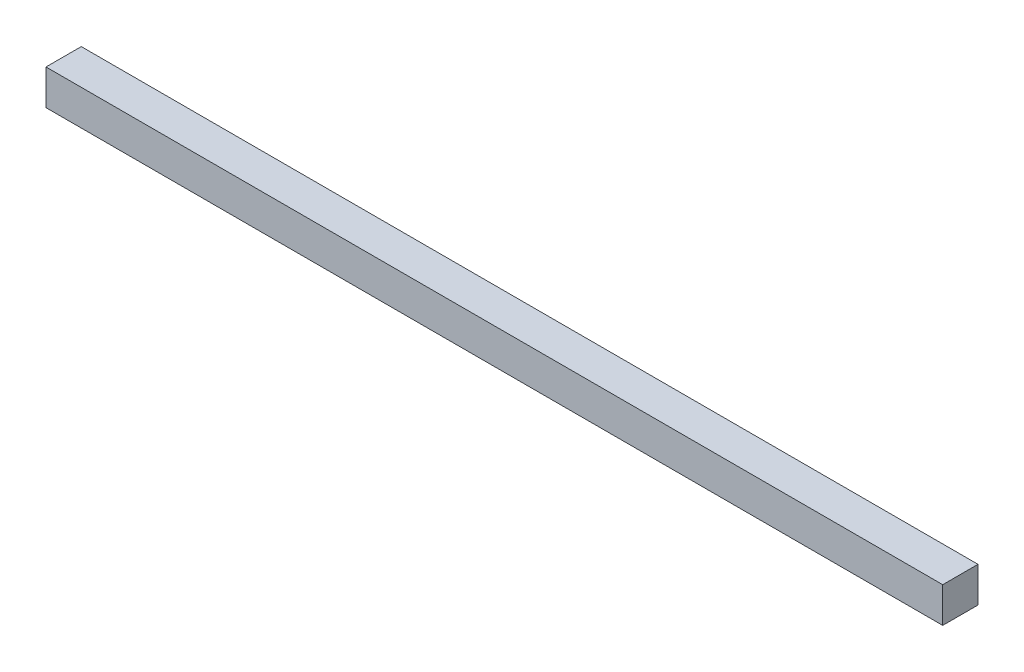
SolidWorks part; units mm, degrees
ref_plane "Front Plane" through (0, 0, 0) normal (0, 0, 1) x (1, 0, 0)
ref_plane "Top Plane" through (0, 0, 0) normal (0, 1, 0) x (1, 0, 0)
ref_plane "Right Plane" through (0, 0, 0) normal (1, 0, 0) x (0, 0, -1)
sketch "Sketch1" plane through (0, 0, 0) normal (0, 0, 1) x (1, 0, 0)
  line L1 (0, 0) -> (76.25, 0)
  line L2 (0, 0) -> (0, 3)
  line L3 (0, 3) -> (76.25, 3)
  line L4 (76.25, 0) -> (76.25, 3)
  dimension "D1" = 76.25
  dimension "D2" = 3
extrude "Boss-Extrude1" add sketch "Sketch1" along normal blind 3
